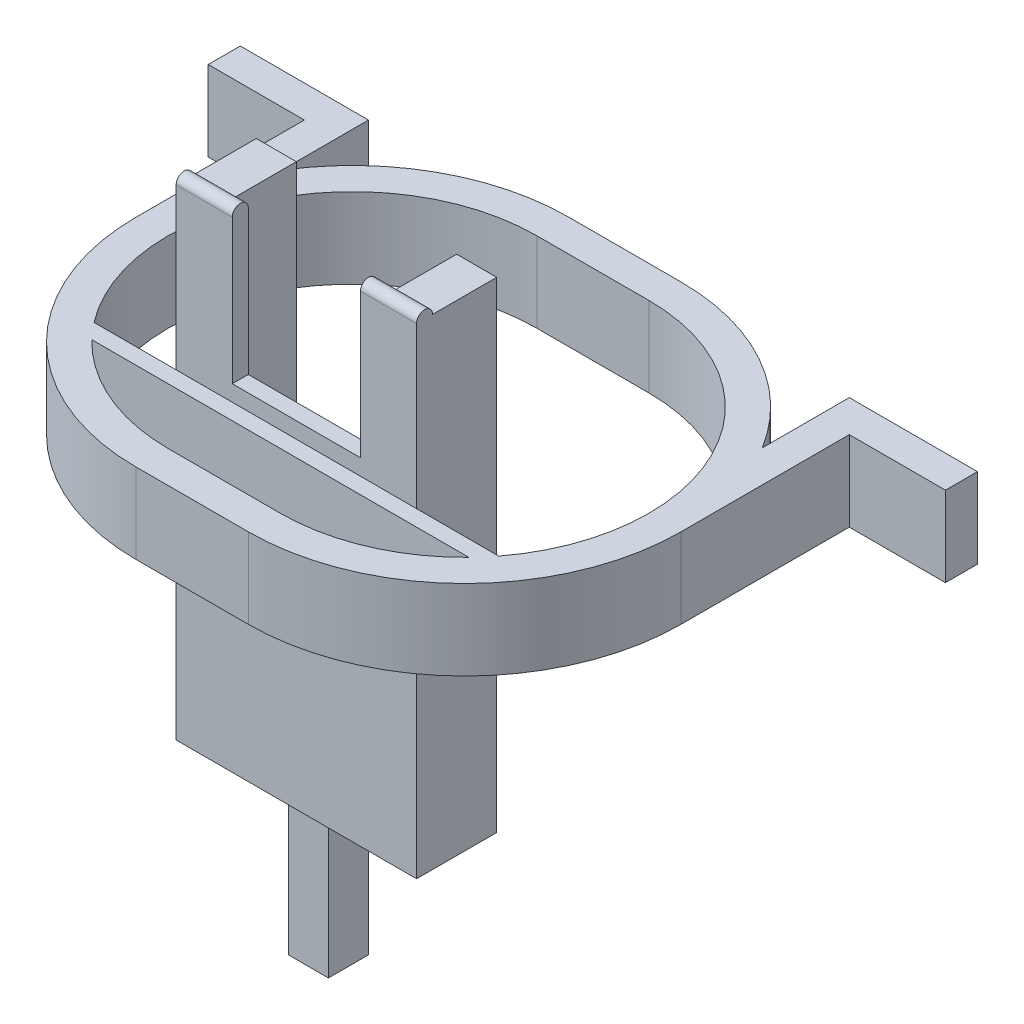
SolidWorks part; units mm, degrees
ref_plane "Front" through (0, 0, 0) normal (0, 0, 1) x (1, 0, 0)
ref_plane "Top" through (0, 0, 0) normal (0, 1, 0) x (1, 0, 0)
ref_plane "Right" through (0, 0, 0) normal (1, 0, 0) x (0, 0, -1)
sketch "草图2" plane through (0, 0, 0) normal (0, 1, 0) x (1, 0, 0)
  line L0 (-7, 0) -> (7, 0) construction
  line L1 (-7, 23) -> (7, 23)
  line L2 (-7, -23) -> (7, -23)
  line L3 (-7, 0) -> (7, 0) construction
  line L4 (-7, 27) -> (7, 27)
  line L5 (-7, -27) -> (7, -27)
  line L6 (-38.2984, -16) -> (40.8516, -16) construction
  line L7 (-23.5227, -16) -> (23.5227, -16)
  line L8 (-35.4759, -14) -> (35.6561, -14) construction
  line L9 (-25.2483, -14) -> (25.2483, -14)
  arc A2 (-7, 23) -> (-25.2483, -14) centre (-7, 0) ccw
  arc A3 (7, -23) -> (23.5227, -16) centre (7, 0) ccw
  arc A4 (-7, 27) -> (-7, -27) centre (-7, 0) ccw
  arc A5 (7, -27) -> (7, 27) centre (7, 0) ccw
  arc A6 (-23.5227, -16) -> (-7, -23) centre (-7, 0) ccw
  arc A7 (25.2483, -14) -> (7, 23) centre (7, 0) ccw
  point P3 (0, 0)
  point P10 (0, 0)
  dimension "D1" = 16
  dimension "D2" = 2
extrude "凸台-拉伸1" add sketch "草图2" along normal blind 10
sketch "草图3" plane through (0, 0, 14) normal (0, 0, -1) x (-1, 0, 0)
  line L1 (-15, -30) -> (15, -30)
  line L2 (-15, -30) -> (-15, 30)
  line L3 (-15, 30) -> (15, 30)
  line L4 (15, -30) -> (15, 30)
  line L5 (0, 0) -> (0, 62.8445) construction
  line L6 (7, 0) -> (34, 0) construction
  dimension "D1" = 30
  dimension "D2" = 60
  dimension "D3" = 15
  dimension "D4" = 30
extrude "凸台-拉伸2" add sketch "草图3" along normal blind 10
sketch "草图7" plane through (-15, 0, 0) normal (-1, 0, 0) x (0, 0, 1)
  line L0 (4, 30) -> (14, 30) construction
  line L1 (4, -30) -> (4, 30) construction
  circle A0 centre (13, 30) radius 1
  dimension "D1" = 9
extrude "凸台-拉伸4" add sketch "草图7" against normal blind 30
sketch "草图6" plane through (0, 0, 4) normal (0, 0, -1) x (-1, 0, 0)
  line L0 (15, 30) -> (-15, 30) construction
  line L1 (-8, 61.2828) -> (8, 61.2828)
  line L2 (-8, 61.2828) -> (-8, 12)
  line L3 (-8, 12) -> (8, 12)
  line L4 (8, 61.2828) -> (8, 12)
  dimension "D1" = 16
  dimension "D2" = 8
  dimension "D3" = 18
extrude "切除-拉伸2" cut sketch "草图6" against normal through all
sketch "草图8" plane through (0, 0, 4) normal (0, 0, -1) x (-1, 0, 0)
  line L1 (-10, -36.1762) -> (10, -36.1762)
  line L2 (-10, -36.1762) -> (-10, 32.4781)
  line L3 (-10, 32.4781) -> (10, 32.4781)
  line L4 (10, -36.1762) -> (10, 32.4781)
  dimension "D1" = 20
  dimension "D2" = 10
extrude "切除-拉伸3" cut sketch "草图8" against normal blind 8
sketch "草图10" plane through (0, -30, 0) normal (0, -1, 0) x (1, 0, 0)
  line L0 (-10, 12) -> (10, 12) construction
  line L2 (-2.5, 12) -> (-2.5, 7.5)
  line L3 (-2.5, 7.5) -> (2.5, 7.5)
  line L4 (2.5, 12) -> (2.5, 7.5)
  line L5 (0, 0) -> (0, 17.6605) construction
  line L6 (-2, 12) -> (-2, 8) construction
  line L8 (-2, 12) -> (-2, 8)
  line L9 (-2, 8) -> (2, 8)
  line L10 (2, 12) -> (2, 8)
  line L13 (-2, 12) -> (2, 12)
  line L14 (-2.5, 12) -> (-2.5, 12.5)
  line L15 (-2.5, 12.5) -> (2.5, 12.5)
  line L16 (2.5, 12) -> (2.5, 12.5)
  dimension "D1" = 5
  dimension "D2" = 4.5
  dimension "D3" = 2.5
  dimension "D4" = 0.5
sketch "草图12" plane through (0, 0, 12) normal (0, 0, -1) x (-1, 0, 0)
  line L0 (-2.5, -8.1968) -> (-2.5, -45.7217)
sweep "扫描2" add profiles "草图10" path "草图12"
sketch "草图16" plane through (0, -45.7217, 0) normal (0, -1, 0) x (1, 0, 0)
  line L1 (-2.5, 12.5) -> (2.5, 12.5)
  line L2 (-2.5, 12.5) -> (-2.5, 7.5)
  line L3 (-2.5, 7.5) -> (2.5, 7.5)
  line L4 (2.5, 12.5) -> (2.5, 7.5)
extrude "凸台-拉伸5" add sketch "草图16" along normal blind 2
sketch "草图17" plane through (0, 10, 0) normal (0, 1, 0) x (1, 0, 0)
  line L0 (-34, 0) -> (36.9862, 0) construction
  line L1 (0, 0) -> (0, 8.4781) construction
  line L2 (-30, 0) -> (-34, 0)
  line L3 (-30, 0) -> (-30, 25)
  line L4 (-30, 25) -> (-34, 25)
  line L5 (-34, 0) -> (-34, 25)
  line L6 (30, 0) -> (34, 0)
  line L7 (30, 0) -> (30, 25)
  line L8 (30, 25) -> (34, 25)
  line L9 (34, 0) -> (34, 25)
  arc A0 (-7, 27) -> (-7, -27) centre (-7, 0) ccw construction
  dimension "D1" = 30
  dimension "D2" = 4
  dimension "D3" = 25
  dimension "D4" = 30
  dimension "D5" = 4
  dimension "D6" = 25
extrude "凸台-拉伸6" add sketch "草图17" against normal blind 10
sketch "草图18" plane through (0, 10, 0) normal (0, 1, 0) x (1, 0, 0)
  line L0 (-46, 25) -> (46, 25) construction
  line L1 (-34, 25) -> (-34, 0) construction
  line L2 (-46, 25) -> (-34, 25)
  line L3 (-46, 25) -> (-46, 21)
  line L4 (-46, 21) -> (-34, 21)
  line L5 (-34, 25) -> (-34, 21)
  line L7 (34, 25) -> (46, 25)
  line L8 (34, 25) -> (34, 21)
  line L9 (34, 21) -> (46, 21)
  line L10 (46, 25) -> (46, 21)
  dimension "D1" = 92
  dimension "D2" = 46
  dimension "D3" = 4
  dimension "D4" = 4
extrude "凸台-拉伸7" add sketch "草图18" against normal blind 10
